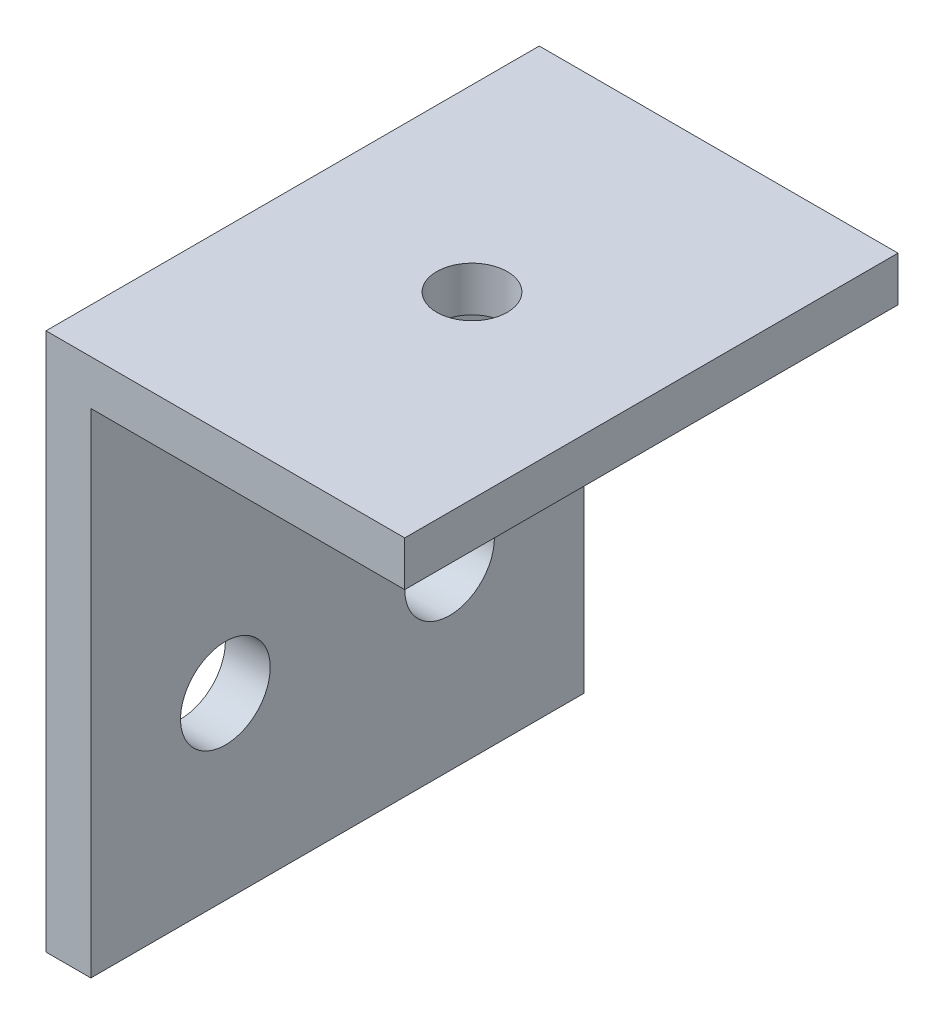
SolidWorks part; units mm, degrees
ref_plane "Front Plane" through (0, 0, 0) normal (0, 0, 1) x (1, 0, 0)
ref_plane "Top Plane" through (0, 0, 0) normal (0, 1, 0) x (1, 0, 0)
ref_plane "Right Plane" through (0, 0, 0) normal (1, 0, 0) x (0, 0, -1)
sketch "Sketch1" plane through (0, 0, 0) normal (0, 0, 1) x (1, 0, 0)
  line L1 (0, 0) -> (3.175, 0)
  line L2 (0, 0) -> (0, 38.1)
  line L3 (0, 38.1) -> (25.4, 38.1)
  line L4 (25.4, 34.925) -> (25.4, 38.1)
  line L7 (25.4, 34.925) -> (3.175, 34.925)
  line L8 (3.175, 0) -> (3.175, 34.925)
  dimension "D1" = 38.1
  dimension "D2" = 25.4
  dimension "D3" = 3.175
  dimension "D4" = 3.175
extrude "Boss-Extrude1" add sketch "Sketch1" along normal blind 34.925
sketch "Sketch2" plane through (3.175, 0, 0) normal (1, 0, 0) x (0, 0, -1)
  line L0 (-34.925, 0) -> (0, 0) construction
  line L1 (-34.925, 0) -> (-34.925, 34.925) construction
  line L2 (0, 0) -> (0, 34.925) construction
  circle A0 centre (-25.4, 12.7) radius 3.175
  circle A1 centre (-9.525, 12.7) radius 3.175
  dimension "D1" = 6.35
  dimension "D2" = 12.7
  dimension "D3" = 9.525
  dimension "D4" = 9.525
extrude "Cut-Extrude1" cut sketch "Sketch2" against normal through all
sketch "Sketch3" plane through (0, 38.1, 0) normal (0, 1, 0) x (1, 0, 0)
  line L0 (25.4, 0) -> (0, 0) construction
  line L1 (0, -34.925) -> (0, 0) construction
  circle A0 centre (12.7, -17.4625) radius 2.5
  dimension "D1" = 5
  dimension "D2" = 12.7
  dimension "D3" = 17.4625
extrude "Cut-Extrude2" cut sketch "Sketch3" against normal through all
